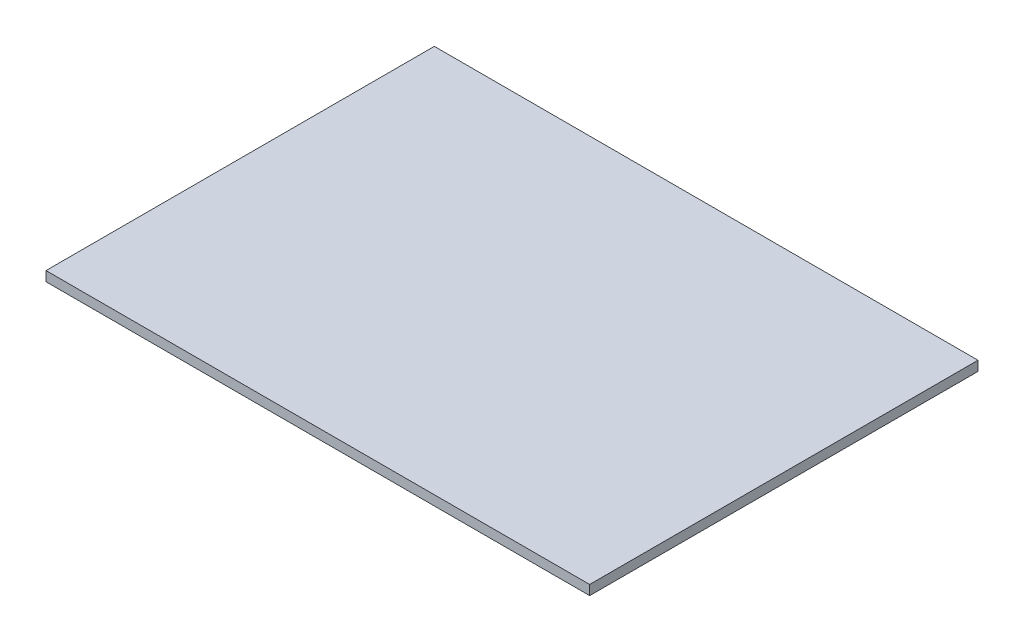
SolidWorks part; units mm, degrees
ref_plane "Front Plane" through (0, 0, 0) normal (0, 0, 1) x (1, 0, 0)
ref_plane "Top Plane" through (0, 0, 0) normal (0, 1, 0) x (1, 0, 0)
ref_plane "Right Plane" through (0, 0, 0) normal (1, 0, 0) x (0, 0, -1)
sketch "Sketch1" plane through (0, 0, 0) normal (0, 1, 0) x (1, 0, 0)
  line L1 (0, 0) -> (355.6, 0)
  line L2 (0, 0) -> (0, 254)
  line L3 (0, 254) -> (355.6, 254)
  line L4 (355.6, 0) -> (355.6, 254)
  dimension "D1" = 355.6
  dimension "D2" = 254
extrude "Boss-Extrude1" add sketch "Sketch1" along normal blind 6.35
